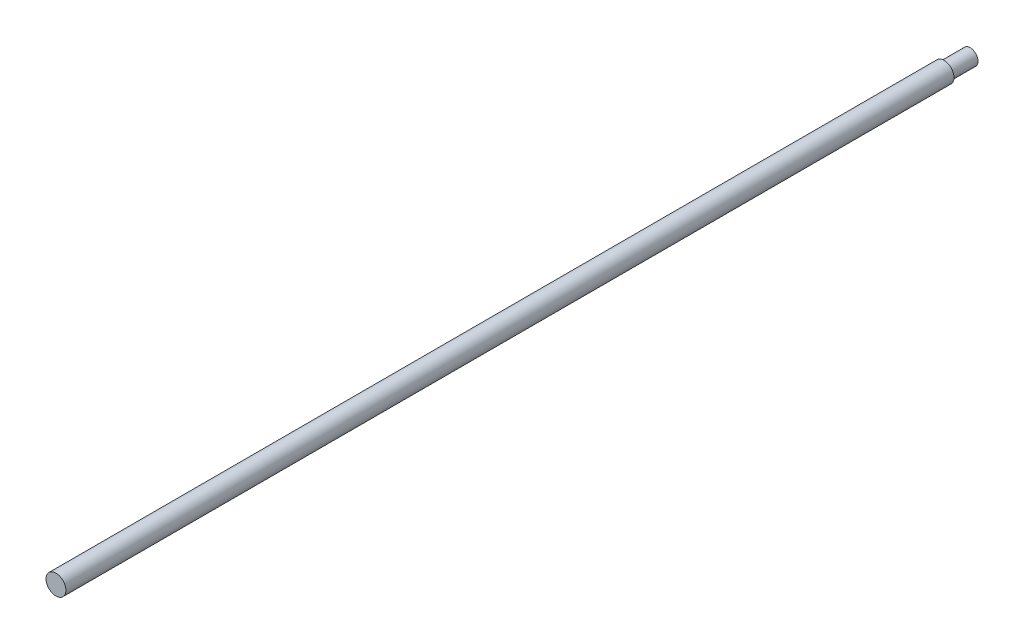
SolidWorks part; units mm, degrees
ref_plane "Front Plane" through (0, 0, 0) normal (0, 0, 1) x (1, 0, 0)
ref_plane "Top Plane" through (0, 0, 0) normal (0, 1, 0) x (1, 0, 0)
ref_plane "Right Plane" through (0, 0, 0) normal (1, 0, 0) x (0, 0, -1)
sketch "Sketch1" plane through (0, 0, 0) normal (0, 0, 1) x (1, 0, 0)
  circle A0 centre (0, 0) radius 3.8
  dimension "D1" = 7.6
extrude "Boss-Extrude1" add sketch "Sketch1" along normal blind 350
sketch "Sketch2" plane through (0, 0, 0) normal (0, 0, -1) x (-1, 0, 0)
  circle A0 centre (0, 0) radius 3
  dimension "D1" = 6
extrude "Cut-Extrude1" cut sketch "Sketch2" against normal blind 10 flip side to cut
